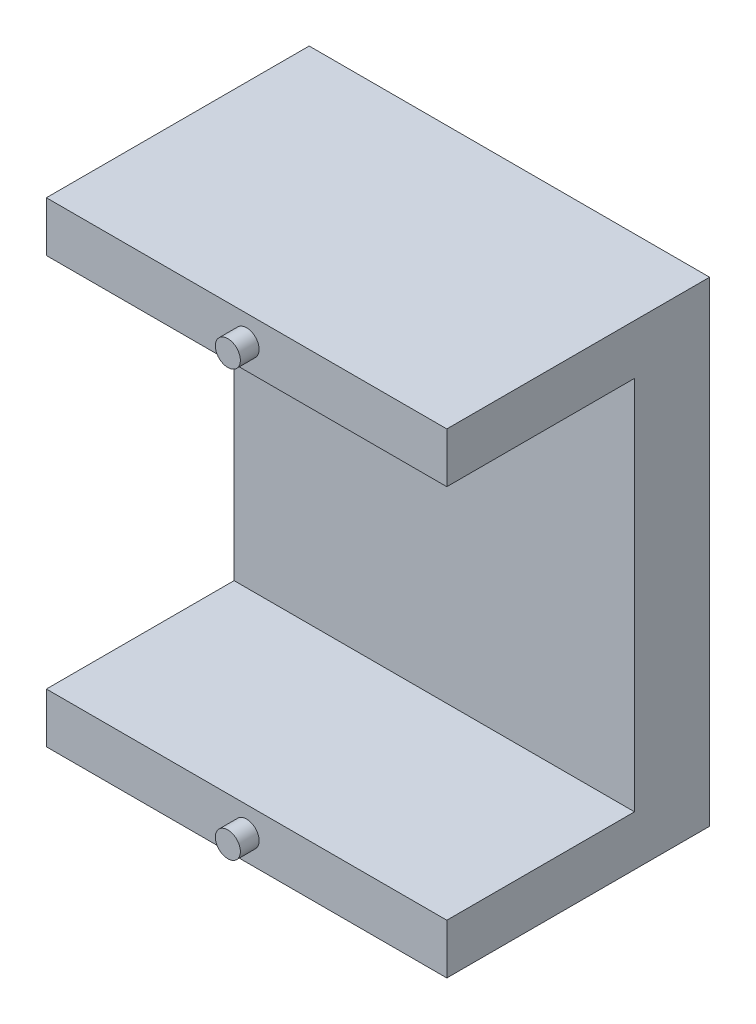
SolidWorks part; units mm, degrees
ref_plane "Front Plane" through (0, 0, 0) normal (0, 0, 1) x (1, 0, 0)
ref_plane "Top Plane" through (0, 0, 0) normal (0, 1, 0) x (1, 0, 0)
ref_plane "Right Plane" through (0, 0, 0) normal (1, 0, 0) x (0, 0, -1)
sketch "Sketch3" plane through (0, 0, 0) normal (1, 0, 0) x (0, 0, -1)
  line L0 (0, 0) -> (0, 4)
  line L1 (0, 4) -> (15, 4)
  line L2 (15, 4) -> (15, 34)
  line L3 (15, 34) -> (0, 34)
  line L4 (0, 34) -> (0, 38)
  line L5 (0, 38) -> (21, 38)
  line L6 (21, 38) -> (21, 0)
  line L7 (21, 0) -> (0, 0)
  dimension "D1" = 21
  dimension "D2" = 38
  dimension "D3" = 4
  dimension "D4" = 4
  dimension "D5" = 15
extrude "Boss-Extrude1" add sketch "Sketch3" along normal mid plane 32 contours L2 L3 L4 L5 L6 L7 L0 L1
sketch "Sketch4" plane through (0, 0, 0) normal (0, 0, 1) x (1, 0, 0)
  line L0 (16, 34) -> (-16, 34) construction
  line L1 (16, 4) -> (-16, 4) construction
  circle A0 centre (0, 36) radius 1
  circle A1 centre (0, 2) radius 1
  dimension "D1" = 2
  dimension "D3" = 2
  dimension "D2" = 2
  dimension "D4" = 2
extrude "Boss-Extrude2" add sketch "Sketch4" along normal mid plane 3
